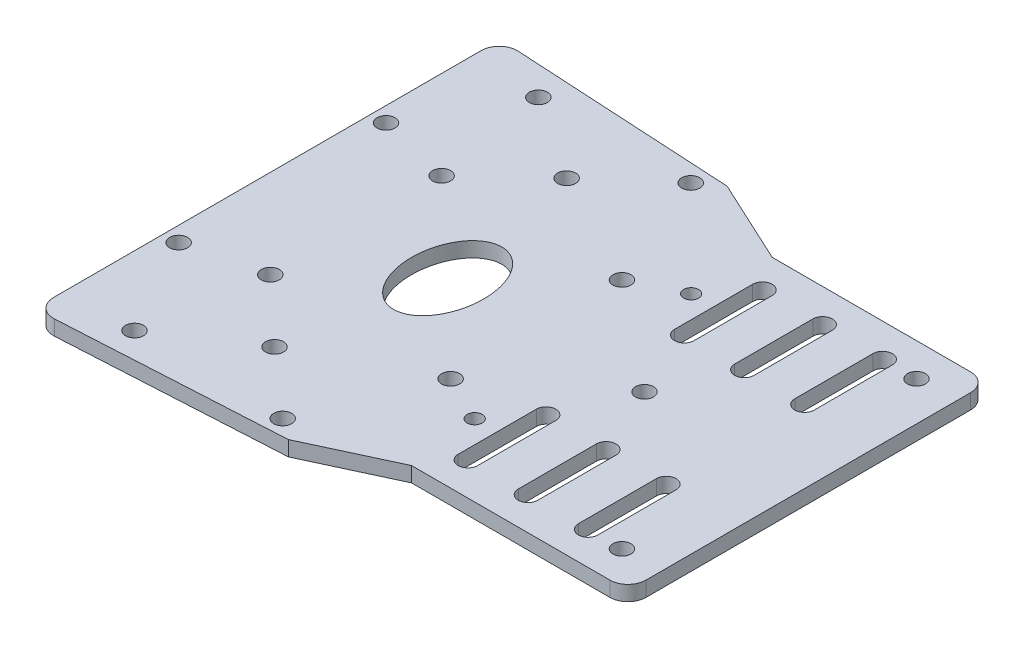
SolidWorks part; units mm, degrees
ref_plane "Alzado" through (0, 0, 0) normal (0, 0, 1) x (1, 0, 0)
ref_plane "Planta" through (0, 0, 0) normal (0, 1, 0) x (1, 0, 0)
ref_plane "Vista lateral" through (0, 0, 0) normal (1, 0, 0) x (0, 0, -1)
sketch "Croquis1" plane through (0, 0, 0) normal (0, 1, 0) x (1, 0, 0)
  line L0 (13, 24.5) -> (13, 26.7085) construction
  line L1 (15, -30) -> (-18, -30)
  line L2 (18, -27) -> (18, 27)
  line L3 (15, 30) -> (-18, 30)
  line L5 (18, -30) -> (-18, 30) construction
  line L6 (18, 30) -> (-18, -30) construction
  line L7 (11.5, 26) -> (11.738, 26) construction
  line L8 (0, 0) -> (34.2953, 0) construction
  line L9 (13, -24.5) -> (18, -24.5) construction
  line L10 (11.5, 24.5) -> (5.875, 24.5) construction
  line L11 (5.875, 24.5) -> (5.875, 11.5) construction
  line L12 (7.5, 24.5) -> (7.5, 11.5)
  line L13 (4.25, 24.5) -> (4.25, 11.5)
  line L14 (10, 24.5) -> (10, 21.7173) construction
  line L15 (5.875, -24.5) -> (5.875, -11.5) construction
  line L16 (7.5, -24.5) -> (7.5, -11.5)
  line L17 (4.25, -24.5) -> (4.25, -11.5)
  line L18 (-4.125, 24.5) -> (-4.125, 11.5) construction
  line L19 (-2.5, 24.5) -> (-2.5, 11.5)
  line L20 (-5.75, 24.5) -> (-5.75, 11.5)
  line L21 (-14.125, 24.5) -> (-14.125, 11.5) construction
  line L22 (-12.5, 24.5) -> (-12.5, 11.5)
  line L23 (-15.75, 24.5) -> (-15.75, 11.5)
  line L24 (-4.125, -24.5) -> (-4.125, -11.5) construction
  line L25 (-2.5, -24.5) -> (-2.5, -11.5)
  line L26 (-5.75, -24.5) -> (-5.75, -11.5)
  line L27 (-14.125, -24.5) -> (-14.125, -11.5) construction
  line L28 (-12.5, -24.5) -> (-12.5, -11.5)
  line L29 (-15.75, -24.5) -> (-15.75, -11.5)
  line L30 (-7.75, 0) -> (-7.75, -0.5168) construction
  line L32 (-32, 36.5) -> (-18, 30)
  line L33 (-18, -30) -> (-32, -36.5)
  line L34 (-18.25, 18) -> (-18.25, 18.8182) construction
  line L35 (-25.75, -14.25) -> (-25.75, -15.75) construction
  line L36 (-27.25, -15.75) -> (-23.0477, -15.75) construction
  line L37 (-19.5, -16.75) -> (-23.5048, -16.75) construction
  line L38 (-72, 35.5765) -> (-72, -35.5765)
  line L39 (-68.8315, 38.5718) -> (-32, 36.5)
  line L40 (-68.8315, -38.5718) -> (-32, -36.5)
  line L41 (-35.5, -35.4449) -> (-30.9795, -35.4449) construction
  line L42 (-34, -33.9449) -> (-34, -32.2963) construction
  line L43 (-45, -24.2974) -> (-45, -16.4604) construction
  line L44 (-46.5, -25.7974) -> (-43.8754, -25.7974) construction
  line L45 (-59, -33.5984) -> (-59, -31.2271) construction
  line L46 (-60.5, -35.0984) -> (-56.5816, -35.0984) construction
  line L47 (-57.25, 15.75) -> (-63.8634, 15.75) construction
  line L48 (-69.5, 17.25) -> (-58.75, 17.25) construction
  line L49 (-55.75, 14.25) -> (-55.75, 12.3618) construction
  line L50 (-28.75, 14.25) -> (-28.75, 12.1071) construction
  line L51 (-71, 17.25) -> (-71, 13.5066) construction
  line L52 (-32, 36.5) -> (-85.6448, 36.5) construction
  circle A0 centre (11.5, 24.5) radius 1.5
  circle A1 centre (11.5, -24.5) radius 1.5
  arc A2 (7.5, 24.5) -> (4.25, 24.5) centre (5.875, 24.5) ccw
  arc A3 (4.25, 11.5) -> (7.5, 11.5) centre (5.875, 11.5) ccw
  arc A4 (7.5, -24.5) -> (4.25, -24.5) centre (5.875, -24.5) cw
  arc A5 (4.25, -11.5) -> (7.5, -11.5) centre (5.875, -11.5) cw
  arc A6 (-2.5, 24.5) -> (-5.75, 24.5) centre (-4.125, 24.5) ccw
  arc A7 (-5.75, 11.5) -> (-2.5, 11.5) centre (-4.125, 11.5) ccw
  arc A8 (-12.5, 24.5) -> (-15.75, 24.5) centre (-14.125, 24.5) ccw
  arc A9 (-15.75, 11.5) -> (-12.5, 11.5) centre (-14.125, 11.5) ccw
  arc A10 (-2.5, -24.5) -> (-5.75, -24.5) centre (-4.125, -24.5) cw
  arc A11 (-5.75, -11.5) -> (-2.5, -11.5) centre (-4.125, -11.5) cw
  arc A12 (-12.5, -24.5) -> (-15.75, -24.5) centre (-14.125, -24.5) cw
  arc A13 (-15.75, -11.5) -> (-12.5, -11.5) centre (-14.125, -11.5) cw
  circle A14 centre (-9.25, 0) radius 1.5
  circle A15 centre (-19.5, 18) radius 1.25
  circle A16 centre (-19.5, -18) radius 1.25
  circle A17 centre (-27.25, -14.25) radius 1.5
  circle A18 centre (-27.25, 14.25) radius 1.5
  arc A19 (18, 27) -> (15, 30) centre (15, 27) ccw
  arc A20 (15, -30) -> (18, -27) centre (15, -27) ccw
  circle A21 centre (-35.5, -33.9449) radius 1.5
  circle A22 centre (-46.5, -24.2974) radius 1.5
  arc A23 (-72, 35.5765) -> (-68.8315, 38.5718) centre (-69, 35.5765) cw
  arc A24 (-72, -35.5765) -> (-68.8315, -38.5718) centre (-69, -35.5765) ccw
  circle A25 centre (-60.5, -33.5984) radius 1.5
  circle A26 centre (-35.5, 33.9449) radius 1.5
  circle A27 centre (-60.5, 33.5984) radius 1.5
  circle A28 centre (-46.5, 24.2974) radius 1.5
  circle A29 centre (-57.25, 14.25) radius 1.5
  circle A31 centre (-69.5, 17.25) radius 1.5
  circle A32 centre (-57.25, -14.25) radius 1.5
  circle A33 centre (-69.5, -17.25) radius 1.5
  ellipse E0 centre (-42, 0) end of major axis (-42, -9) minor radius 6
  point P0 (0, 0)
  point P18 (5.875, 18)
  point P29 (5.875, -18)
  point P34 (-4.125, 18)
  point P41 (-14.125, 18)
  point P52 (-4.125, -18)
  point P59 (-14.125, -18)
  point P66 (-72, 0)
  point P73 (-15.75, 18)
  point P108 (-72, 38.75)
  point P111 (-72, -38.75)
  point P142 (0, 0)
  dimension "D3" = 3
  dimension "D4" = 5
  dimension "D7" = 13
  dimension "D15" = 3
  dimension "D19" = 2.5
  dimension "D21" = 3
  dimension "D23" = 1
  dimension "D24" = 3
  dimension "D30" = 3
  dimension "D32" = 3
  dimension "D34" = 3
  dimension "D37" = 3
  dimension "D39" = 3
  dimension "D41" = 1
  dimension "D40" = 3
  dimension "D1" = 36
  dimension "D2" = 60
  dimension "D5" = 4
  dimension "D6" = 3.25
  dimension "D8" = 2.5
  dimension "D9" = 6.75
  dimension "D10" = 6.75
  dimension "D11" = 3.25
  dimension "D12" = 13
  dimension "D13" = 3.25
  dimension "D14" = 13
  dimension "D16" = 2
  dimension "D17" = 40
  dimension "D18" = 73
  dimension "D20" = 2.5
  dimension "D22" = 10
  dimension "D25" = 77.5
  dimension "D26" = 14
  dimension "D27" = 6.5
  dimension "D28" = 2
  dimension "D29" = 1.25
  dimension "D31" = 11
  dimension "D33" = 11.5
  dimension "D35" = 25
  dimension "D36" = 3
  dimension "D38" = 27
  dimension "D42" = 1.5
  dimension "D43" = 54
  dimension "D44" = 18
  dimension "D45" = 12
extrude "Saliente-Extruir1" add sketch "Croquis1" along normal blind 2.5
